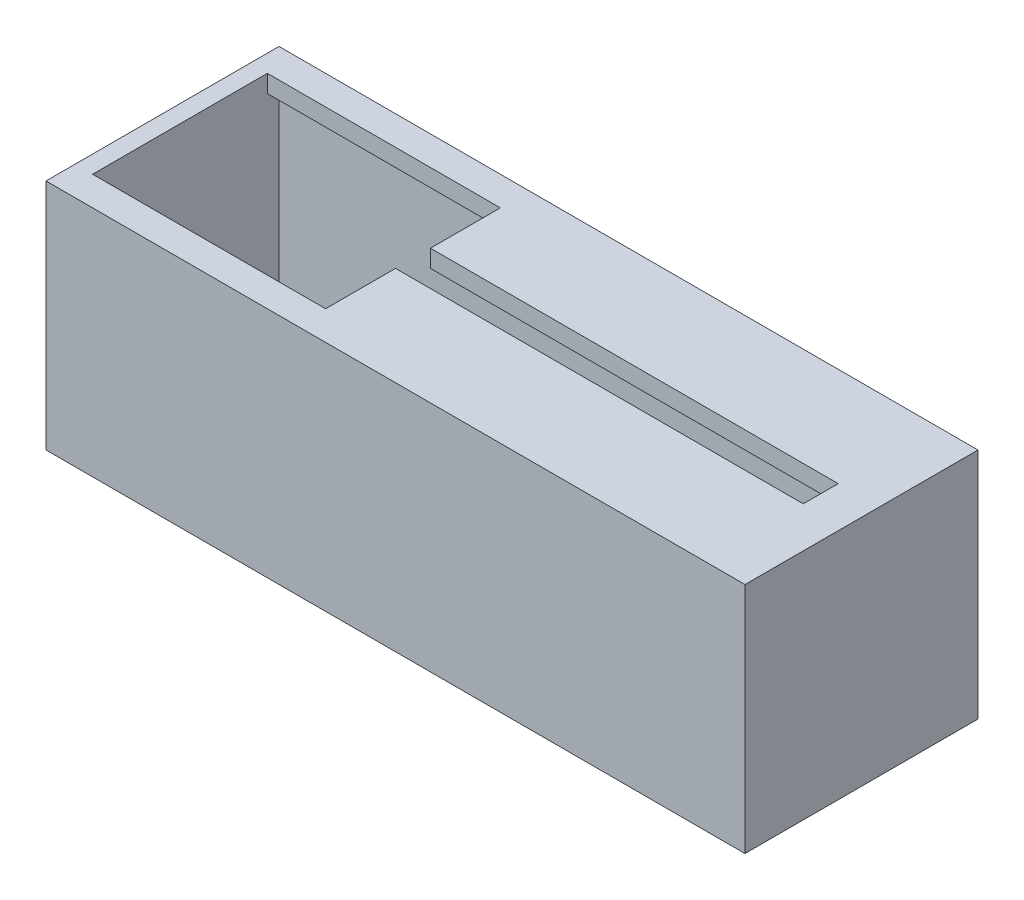
SolidWorks part; units mm, degrees
ref_plane "Alzado" through (0, 0, 0) normal (0, 0, 1) x (1, 0, 0)
ref_plane "Planta" through (0, 0, 0) normal (0, 1, 0) x (1, 0, 0)
ref_plane "Vista lateral" through (0, 0, 0) normal (1, 0, 0) x (0, 0, -1)
sketch "Croquis1" plane through (0, 0, 0) normal (0, 1, 0) x (1, 0, 0)
  line L1 (0, 0) -> (60, 0)
  line L2 (0, 0) -> (0, -20)
  line L3 (0, -20) -> (60, -20)
  line L4 (60, 0) -> (60, -20)
  dimension "D1" = 60
  dimension "D2" = 20
extrude "Saliente-Extruir1" add sketch "Croquis1" along normal blind 20
shell "Vaciado1" thickness 1.5
sketch "Croquis2" plane through (0, 20, 0) normal (0, 1, 0) x (1, 0, 0)
  line L0 (0, -20) -> (60, -20) construction
  line L1 (1.5, -2.5) -> (21.5, -2.5)
  line L2 (1.5, -2.5) -> (1.5, -17.5)
  line L3 (1.5, -17.5) -> (21.5, -17.5)
  line L4 (21.5, -2.5) -> (21.5, -8.5)
  line L9 (0, -11) -> (0, 11) construction
  line L10 (21.5, -11.5) -> (21.5, -17.5)
  line L11 (21.5, -8.5) -> (56.5, -8.5)
  line L13 (21.5, -11.5) -> (56.5, -11.5)
  line L14 (56.5, -8.5) -> (56.5, -11.5)
  dimension "D1" = 15
  dimension "D2" = 20
  dimension "D3" = 2.5
  dimension "D4" = 1.5
  dimension "D5" = 6
  dimension "D6" = 3
  dimension "D7" = 35
extrude "Cortar-Extruir1" cut sketch "Croquis2" against normal blind 18
sketch "Croquis3" plane through (0, 1.5, 0) normal (0, 1, 0) x (1, 0, 0)
  line L1 (1.5, -1.5) -> (1.5, -18.5) construction
  line L2 (58.5, -1.5) -> (1.5, -1.5) construction
  circle A0 centre (4, -10.25) radius 1.25
  dimension "D1" = 2.5
  dimension "D2" = 2.5
  dimension "D3" = 8.75
extrude "Cortar-Extruir2" cut sketch "Croquis3" against normal through all
